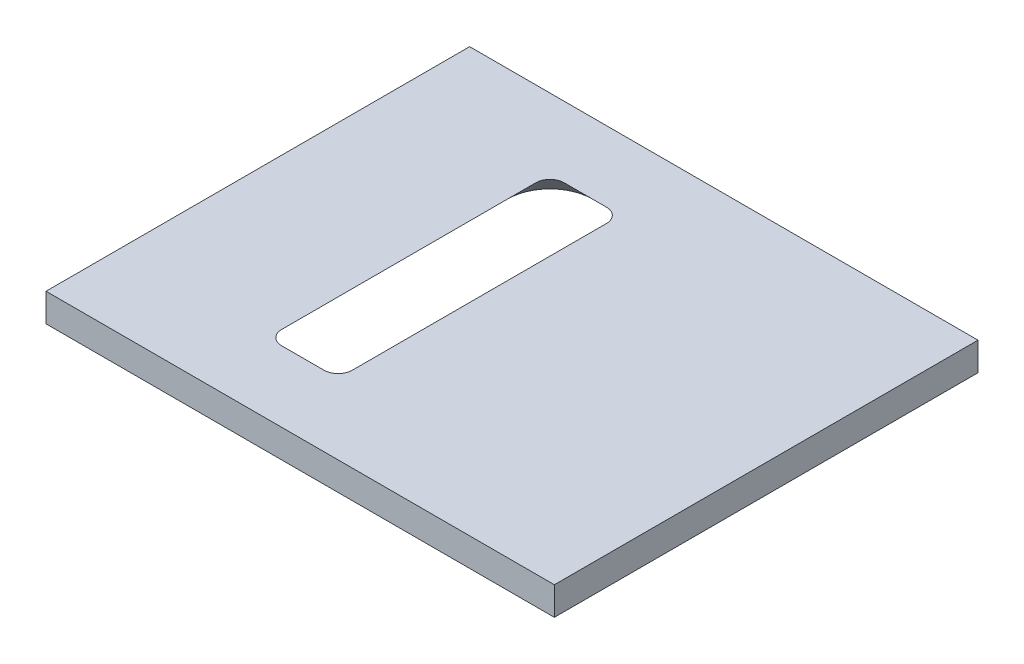
SolidWorks part; units mm, degrees
material "6061-T4 (SS)"
ref_plane "Front Plane" through (0, 0, 0) normal (0, 0, 1) x (1, 0, 0)
ref_plane "Top Plane" through (0, 0, 0) normal (0, 1, 0) x (1, 0, 0)
ref_plane "Right Plane" through (0, 0, 0) normal (1, 0, 0) x (0, 0, -1)
sketch "Sketch2" plane through (0, 0, 0) normal (0, 1, 0) x (1, 0, 0)
  line L5 (-13.189, 15) -> (22.811, 15)
  line L6 (-13.189, 15) -> (-13.189, -15)
  line L7 (-13.189, -15) -> (22.811, -15)
  line L8 (22.811, 15) -> (22.811, -15)
  line L9 (-13.189, 15) -> (22.811, -15) construction
  line L10 (-13.189, -15) -> (22.811, 15) construction
  dimension "D1" = 36
  dimension "D2" = 30
extrude "Boss-Extrude1" add sketch "Sketch2" along normal blind 2
sketch "Sketch4" plane through (0, 2, 0) normal (0, 1, 0) x (1, 0, 0)
  line L1 (1.5, -10) -> (-1.5, -10)
  line L2 (2.5, -9) -> (2.5, 9)
  line L3 (1.5, 10) -> (-1.5, 10)
  line L4 (-2.5, -9) -> (-2.5, 9)
  line L5 (2.5, -10) -> (-2.5, 10) construction
  line L6 (2.5, 10) -> (-2.5, -10) construction
  arc A0 (1.5, -10) -> (2.5, -9) centre (1.5, -9) ccw
  arc A1 (2.5, 9) -> (1.5, 10) centre (1.5, 9) ccw
  arc A2 (-1.5, 10) -> (-2.5, 9) centre (-1.5, 9) ccw
  arc A3 (-1.5, -10) -> (-2.5, -9) centre (-1.5, -9) cw
  point P0 (0, 0)
  dimension "D3" = 1
  dimension "D1" = 20
  dimension "D2" = 5
extrude "Cut-Extrude4" cut sketch "Sketch4" against normal through all draft 45 draft outward yes
sketch "Sketch5" plane through (0, 2, 0) normal (0, 1, 0) x (1, 0, 0)
  line L0 (18.2427, -15) -> (18.2427, 15) construction
  line L1 (-13.189, -15) -> (22.811, -15) construction
  line L2 (22.811, 15) -> (-13.189, 15) construction
  circle A0 centre (18.2427, -10) radius 1.595
  circle A1 centre (18.2427, 10) radius 1.595
  dimension "D3" = 3.19
  dimension "D4" = 3.19
  dimension "D1" = 5
  dimension "D2" = 5
extrude "Cut-Extrude5" [suppressed] cut sketch "Sketch5" against normal through all
